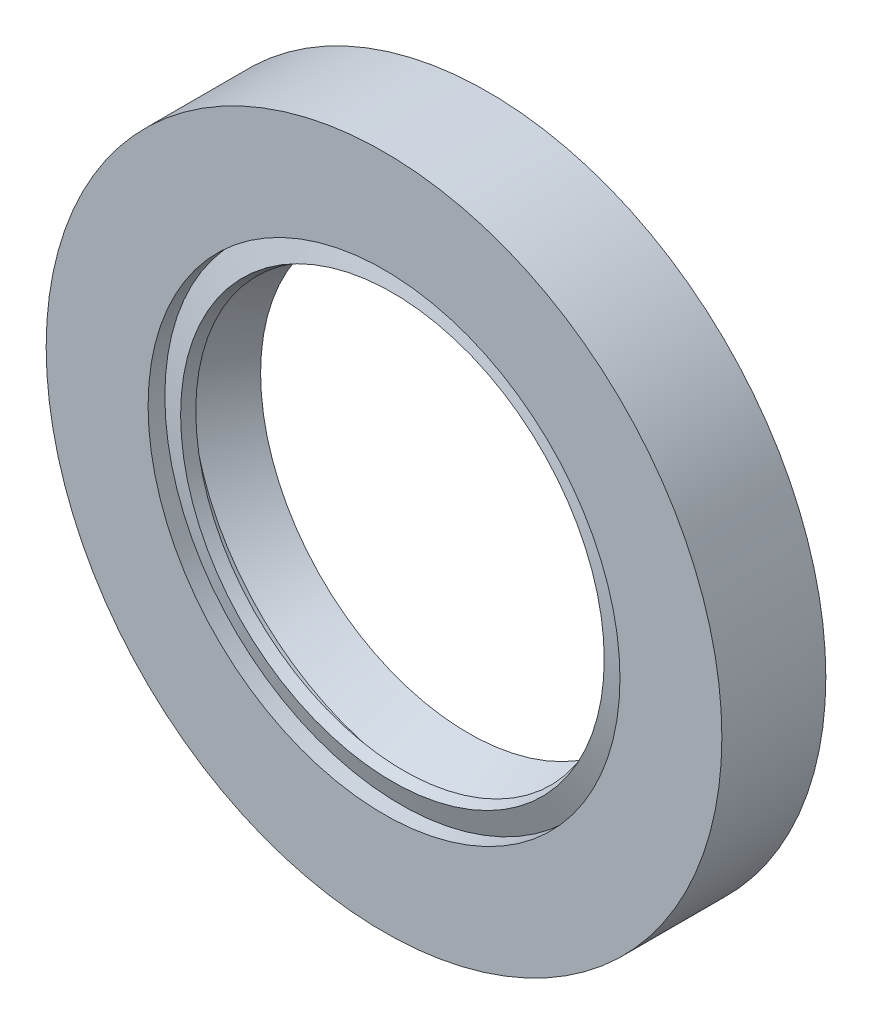
SolidWorks part; units mm, degrees
material "NBR"
ref_plane "Front Plane" through (0, 0, 0) normal (0, 0, 1) x (1, 0, 0)
ref_plane "Top Plane" through (0, 0, 0) normal (0, 1, 0) x (1, 0, 0)
ref_plane "Right Plane" through (0, 0, 0) normal (1, 0, 0) x (0, 0, -1)
sketch "Sketch1" plane through (0, 0, 0) normal (1, 0, 0) x (0, 0, -1)
  line L0 (8, 26) -> (0, 26)
  line L1 (0, 26) -> (0, 18.1571)
  line L2 (0, 18.1571) -> (1.2899, 18.1571)
  line L3 (1.2899, 18.1571) -> (0.6466, 16.3001)
  line L4 (0.6466, 16.3001) -> (1.5127, 16)
  line L5 (1.5127, 16) -> (2.2407, 18.1012)
  line L6 (2.2407, 18.1012) -> (3.2672, 18.1012)
  line L7 (7.7191, 18.1629) -> (7.7191, 19.2561)
  line L8 (7.7191, 19.2561) -> (1.4702, 19.2561)
  line L9 (1.4702, 19.2561) -> (1.4702, 24.2945)
  line L10 (1.4702, 24.2945) -> (8, 24.2945)
  line L11 (8, 24.2945) -> (8, 26)
  line L12 (3.2672, 18.1012) -> (6.5018, 16)
  line L13 (6.5018, 16) -> (7.7191, 18.1629)
  line L14 (0, 0) -> (11.2863, 0) construction
  dimension "D1" = 26
  dimension "D2" = 8
  dimension "D3" = 16
revolve "Revolve1" add sketch "Sketch1" angle 360 about L14
